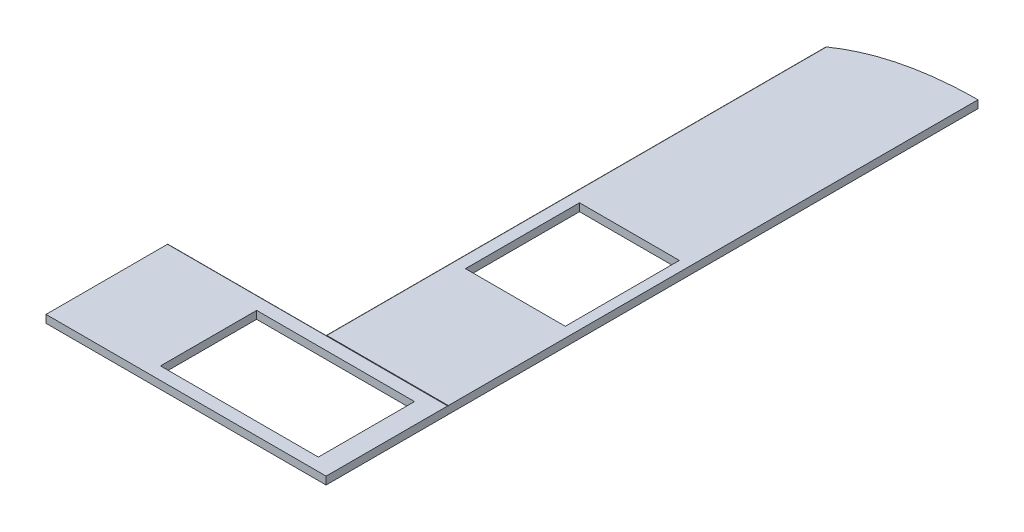
SolidWorks part; units mm, degrees
ref_plane "Front Plane" through (0, 0, 0) normal (0, 0, 1) x (1, 0, 0)
ref_plane "Top Plane" through (0, 0, 0) normal (0, 1, 0) x (1, 0, 0)
ref_plane "Right Plane" through (0, 0, 0) normal (1, 0, 0) x (0, 0, -1)
sketch "Sketch2" plane through (0, 0, 0) normal (1, 0, 0) x (0, 0, -1)
  line L1 (296, -19) -> (-300, -19)
  line L2 (300, -15) -> (300, 15)
  line L3 (296, 19) -> (-300, 19)
  line L4 (-300, -19) -> (-300, 19)
  line L5 (300, -19) -> (-300, 19) construction
  line L6 (300, 19) -> (-300, -19) construction
  arc A0 (296, -19) -> (300, -15) centre (296, -15) ccw
  arc A1 (300, 15) -> (296, 19) centre (296, 15) ccw
  point P0 (0, 0)
  dimension "D3" = 4
  dimension "D1" = 38
  dimension "D2" = 600
extrude "Boss-Extrude1" add sketch "Sketch2" along normal blind 1375
sketch "Sketch3" plane through (0, 0, -300) normal (0, 0, -1) x (-1, 0, 0)
  line L0 (-1375, -19) -> (0, -19) construction
  line L1 (-1375, 19) -> (-779, 19)
  line L2 (-1375, 19) -> (-1375, -19)
  line L3 (-1375, -19) -> (-779, -19)
  line L4 (-775, 15) -> (-775, -15)
  arc A0 (-779, -19) -> (-775, -15) centre (-779, -15) ccw
  arc A1 (-779, 19) -> (-775, 15) centre (-779, 15) cw
  point P9 (-775, -19)
  point P12 (-775, 19)
  dimension "D2" = 4
  dimension "D1" = 600
extrude "Boss-Extrude2" add sketch "Sketch3" along normal blind 2600
sketch "Sketch4" plane through (0, 19, 0) normal (0, 1, 0) x (1, 0, 0)
  line L0 (1275, -238) -> (500, 234) construction
  line L1 (1275, 234) -> (500, 234)
  line L2 (1275, 234) -> (1275, -238)
  line L3 (1275, -238) -> (500, -238)
  line L4 (500, 234) -> (500, -238)
  line L5 (1275, 234) -> (500, -238) construction
  line L6 (549.4488, 296) -> (549.4488, -300) construction
  line L9 (1375, 296) -> (0, 296) construction
  line L10 (1375, -300) -> (0, -300) construction
  line L11 (1375, 296) -> (1375, -300) construction
  point P10 (549.4488, -2)
  point P11 (887.5, -2)
  dimension "D1" = 775
  dimension "D2" = 472
  dimension "D3" = 100
extrude "sink" cut sketch "Sketch4" against normal through all
sketch "Sketch5" plane through (0, 19, 0) normal (0, 1, 0) x (1, 0, 0)
  line L0 (1375, 2900) -> (1375, 300) construction
  line L1 (835, 924) -> (1325, 924)
  line L2 (835, 924) -> (835, 1484)
  line L3 (835, 1484) -> (1325, 1484)
  line L4 (1325, 924) -> (1325, 1484)
  line L5 (835, 924) -> (1325, 1484) construction
  line L6 (835, 1484) -> (1325, 924) construction
  line L7 (1375, -300) -> (0, -300) construction
  point P0 (1080, 1204)
  dimension "D1" = 50
  dimension "D2" = 560
  dimension "D3" = 490
  dimension "D4" = 1224
extrude "panel" cut sketch "Sketch5" against normal through all
sketch "Sketch6" plane through (0, 19, 0) normal (0, 1, 0) x (1, 0, 0)
  line L0 (1025, 2900) -> (1025, 2972.2328)
  line L1 (779, 2900) -> (1375, 2900) construction
  line L2 (775, 2900) -> (775, 300) construction
  line L3 (775, 2650) -> (1025, 2650) construction
  line L4 (1025, 2900) -> (1025, 2650) construction
  line L5 (1025, 2972.2328) -> (232.0197, 2972.2328)
  line L6 (232.0197, 2972.2328) -> (232.0197, 2650)
  line L7 (232.0197, 2650) -> (775, 2650)
  arc A0 (775, 2650) -> (1025, 2900) centre (1025, 2650) cw
  dimension "D1" = 250
extrude "Cut-Extrude1" [suppressed] cut sketch "Sketch6" against normal through all
sketch "Sketch7" plane through (0, 19, 0) normal (0, 1, 0) x (1, 0, 0)
  line L0 (775, 2900) -> (775, 300) construction
  line L1 (779, 2900) -> (1375, 2900) construction
  line L2 (775, 2750) -> (581.0902, 2808.6295)
  line L3 (581.0902, 2808.6295) -> (669.5291, 3022.4285)
  line L4 (669.5291, 3022.4285) -> (1128.0378, 3045.6115)
  line L5 (1128.0378, 3045.6115) -> (1325.3223, 3055.5866)
  line L6 (1325.3223, 3055.5866) -> (1375, 2900)
  spline S0 degree 2 poles (775, 2750) (983.3931, 2898.4166) (1375, 2900) knots 0 0 0 1 1 1
  dimension "D1" = 150
extrude "Cut-Extrude2" cut sketch "Sketch7" against normal through all
equation "\"SHRT_LEN\"= 1375"
equation "\"D1@Boss-Extrude1\"=\"SHRT_LEN\""
equation "\"WIDTH\"=600"
equation "\"D2@Sketch2\"=\"WIDTH\""
equation "\"corner\"=4"
equation "\"D3@Sketch2\"=\"corner\""
equation "\"D1@Sketch3\"=\"WIDTH\""
equation "\"D2@Sketch3\"=\"corner\""
equation "\"LONG_LEN\"= 3200"
equation "\"D1@Boss-Extrude2\"=\"LONG_LEN\"-\"WIDTH\""
equation "\"SINK_WIDTH\"=775"
equation "\"D1@Sketch4\"=\"SINK_WIDTH\""
equation "\"SINK_HEIGHT\"=472"
equation "\"D2@Sketch4\"=\"SINK_HEIGHT\""
equation "\"PANEL_OFFSET\"= 50"
equation "\"D1@Sketch5\"=\"PANEL_OFFSET\""
equation "\"PANEL_WIDTH\"=560"
equation "\"D2@Sketch5\"=\"PANEL_WIDTH\""
equation "\"PANEL_HEIGHT\"=490"
equation "\"D3@Sketch5\"=\"PANEL_HEIGHT\""
equation "\"panel_offset_right\"= 1224"
equation "\"D4@Sketch5\"=\"panel_offset_right\""
equation "\"RADIUS_END\"=250"
equation "\"D1@Sketch6\"=\"RADIUS_END\""
